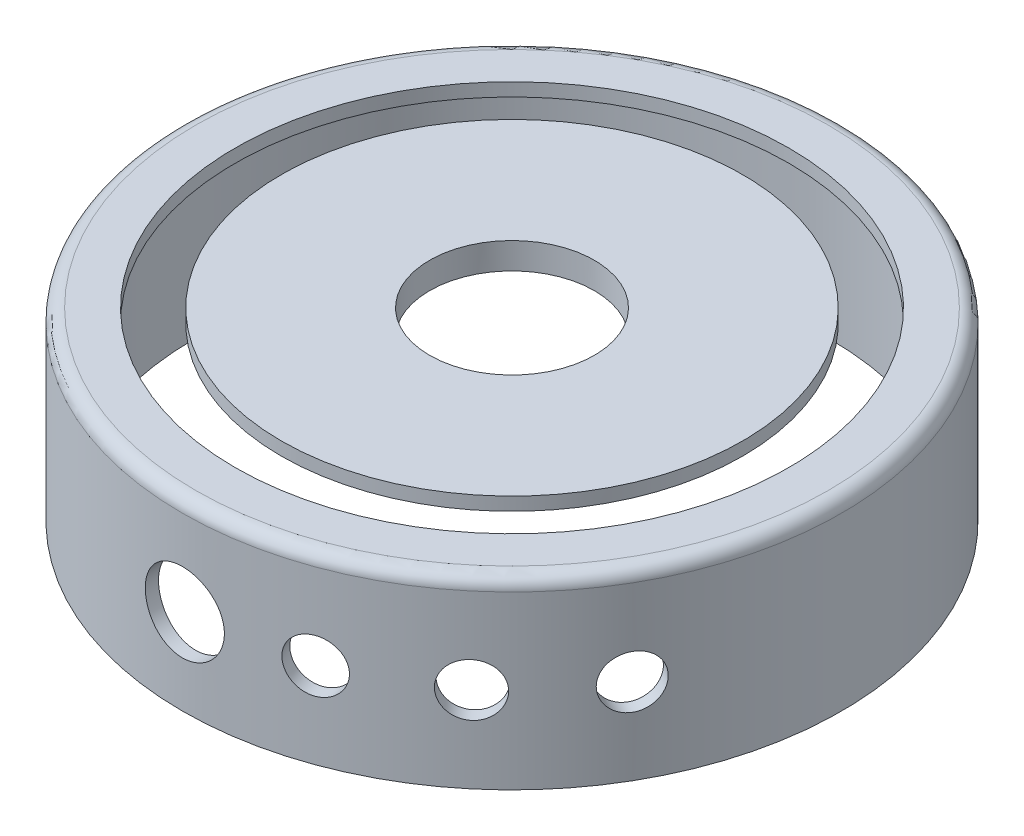
SolidWorks part; units mm, degrees
ref_plane "Front Plane" through (0, 0, 0) normal (0, 0, 1) x (1, 0, 0)
ref_plane "Top Plane" through (0, 0, 0) normal (0, 1, 0) x (1, 0, 0)
ref_plane "Right Plane" through (0, 0, 0) normal (1, 0, 0) x (0, 0, -1)
sketch "Sketch1" plane through (0, 0, 0) normal (0, 1, 0) x (1, 0, 0)
  circle A0 centre (0, 0) radius 50
  dimension "D1" = 100
extrude "Boss-Extrude1" add sketch "Sketch1" along normal blind 28
sketch "Sketch3" plane through (0, 0, 0) normal (0, -1, 0) x (1, 0, 0)
  circle A3 centre (0, 0) radius 48
  circle A4 centre (0, 0) radius 48
  dimension "D1" = 2
extrude "Cut-Extrude1" cut sketch "Sketch3" against normal blind 26
sketch "Sketch4" plane through (0, 28, 0) normal (0, 1, 0) x (1, 0, 0)
  circle A0 centre (0, 0) radius 42
  circle A2 centre (0, 0) radius 50 construction
  circle A3 centre (0, 0) radius 35
  dimension "D1" = 8
  dimension "D2" = 7
extrude "Cut-Extrude2" cut sketch "Sketch4" against normal blind 10 contours A0 A3
sketch "Sketch5" plane through (0, 28, 0) normal (0, 1, 0) x (1, 0, 0)
  circle A0 centre (0, 0) radius 12.5
  dimension "D1" = 25
extrude "Cut-Extrude3" cut sketch "Sketch5" against normal blind 10
fillet "Fillet1" radius 2 1 edges at (0, 28, 50)
sketch "Sketch6" plane through (0, 0, 0) normal (0, 0, 1) x (1, 0, 0)
  line L0 (12.5, 28) -> (-12.5, 28) construction
  circle A0 centre (0, 13) radius 4
  dimension "D1" = 8
  dimension "D2" = 15
extrude "Cut-Extrude4" cut sketch "Sketch6" along normal through all
pattern_circular "CirPattern1" count 4 every 20 about axis through (0, 26, 0) along (0, 1, 0) of "Cut-Extrude4"
sketch "Sketch7" plane through (0, 0, 0) normal (0, 0, 1) x (1, 0, 0)
  circle A0 centre (0, 13) radius 6
  dimension "D1" = 12
extrude "Cut-Extrude5" cut sketch "Sketch7" along normal through all
sketch "Sketch8" plane through (0, 26, 0) normal (0, -1, 0) x (1, 0, 0)
  circle A0 centre (0, 0) radius 13.5
  circle A1 centre (0, 0) radius 12.5 construction
  dimension "D1" = 1
extrude "Boss-Extrude2" add sketch "Sketch8" along normal blind 2
sketch "Sketch9" plane through (0, 24, 0) normal (0, -1, 0) x (1, 0, 0)
  circle A0 centre (0, 0) radius 12.5
  circle A1 centre (0, 0) radius 13.5 construction
  dimension "D1" = 1
extrude "Cut-Extrude6" cut sketch "Sketch9" against normal through all
